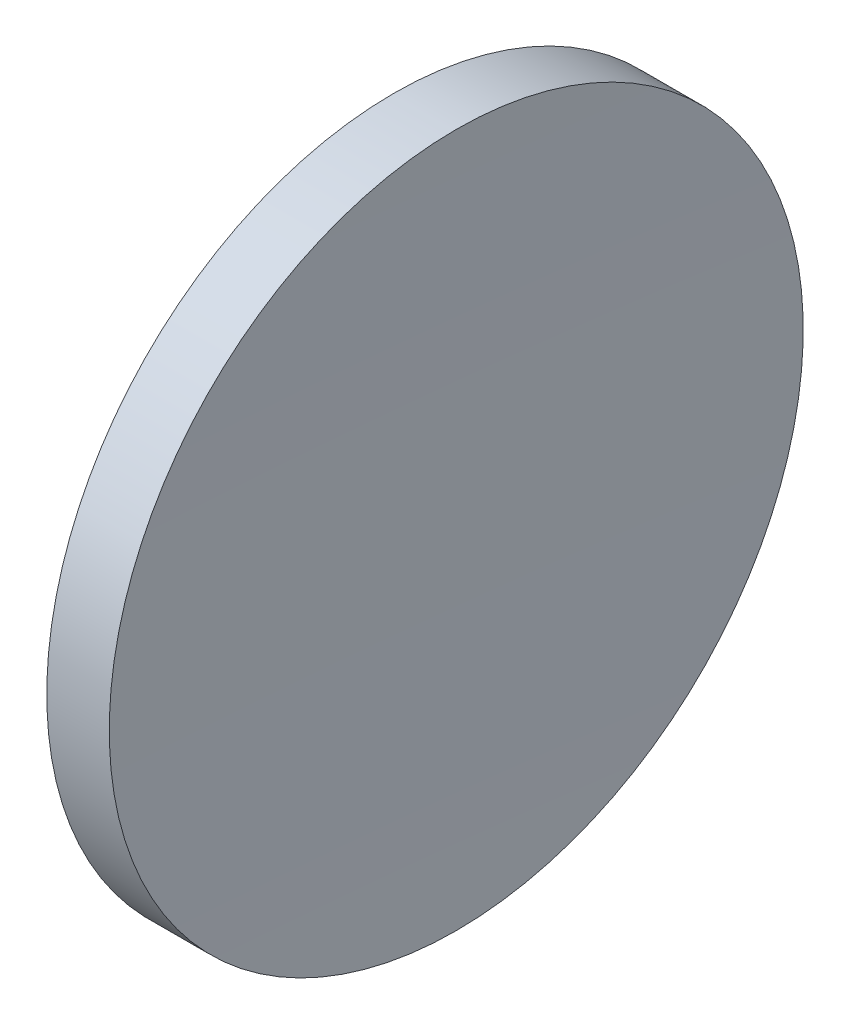
SolidWorks part; units mm, degrees
ref_plane "前视基准面" through (0, 0, 0) normal (0, 0, 1) x (1, 0, 0)
ref_plane "上视基准面" through (0, 0, 0) normal (0, 1, 0) x (1, 0, 0)
ref_plane "右视基准面" through (0, 0, 0) normal (1, 0, 0) x (0, 0, -1)
sketch "草图1" plane through (0, 0, 0) normal (0, 0, 1) x (1, 0, 0)
  line L0 (89.8587, 52.1781) -> (104.0854, 52.1781) construction
  line L1 (95.0904, 52.1781) -> (97.0904, 52.1781)
  line L3 (96.0904, 64.8781) -> (97.2341, 64.8781)
  line L4 (96.0904, 64.8781) -> (94.9468, 64.8781)
  arc A0 (95.0904, 52.1781) -> (94.9468, 64.8781) centre (-466.5096, 52.1781) ccw
  arc A1 (97.2341, 64.8781) -> (97.0904, 52.1781) centre (658.6904, 52.1781) ccw
revolve "旋转1" add sketch "草图1" angle 360 about L0
